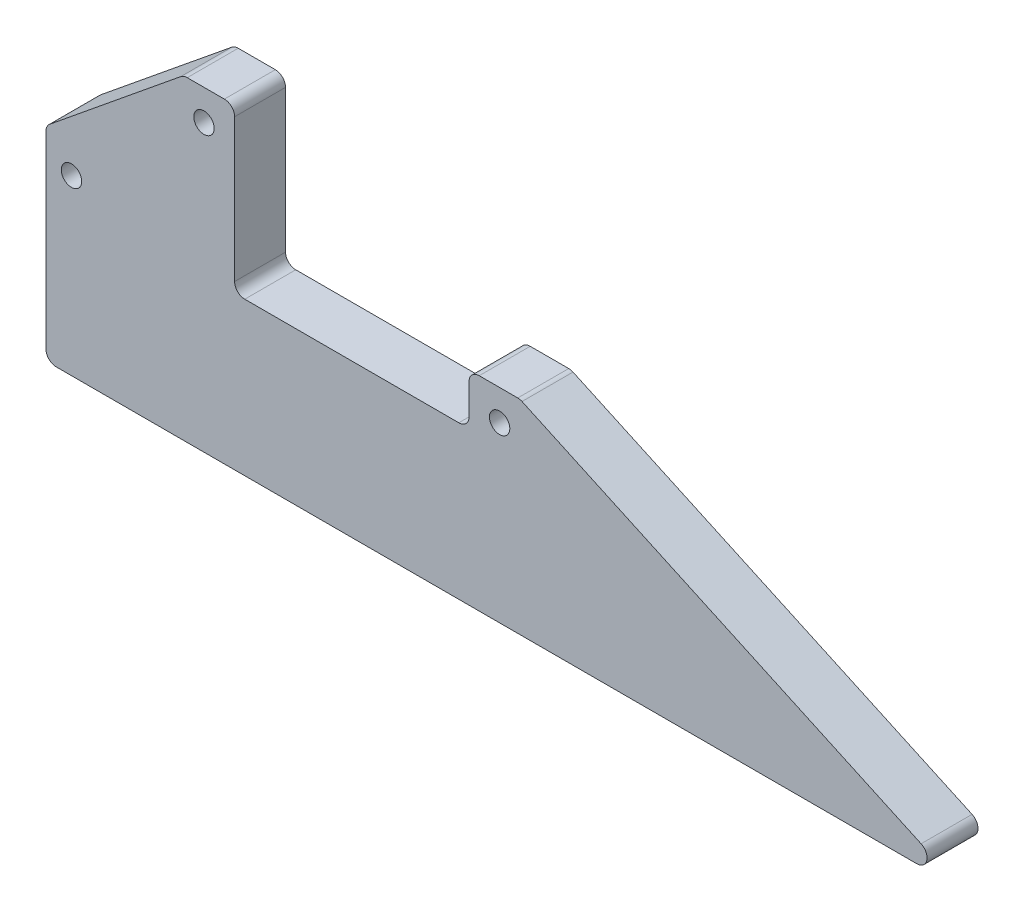
SolidWorks part; units mm, degrees
ref_plane "Front Plane" through (0, 0, 0) normal (0, 0, 1) x (1, 0, 0)
ref_plane "Top Plane" through (0, 0, 0) normal (0, 1, 0) x (1, 0, 0)
ref_plane "Right Plane" through (0, 0, 0) normal (1, 0, 0) x (0, 0, -1)
sketch "Sketch1" plane through (0, 0, 0) normal (0, 0, 1) x (1, 0, 0)
  line L1 (-87, 40) -> (0, 0)
  line L2 (0, 0) -> (-180, 0)
  line L4 (-153, 62) -> (-143, 62)
  line L5 (-143, 62) -> (-143, 30)
  line L6 (-143, 30) -> (-97, 30)
  line L7 (-97, 30) -> (-97, 40)
  line L8 (-97, 40) -> (-87, 40)
  line L9 (-153, 62) -> (-180, 40)
  line L10 (-180, 40) -> (-180, 0)
  point P3 (0, 0)
  dimension "D1" = 37
  dimension "D2" = 10
  dimension "D3" = 32
  dimension "D4" = 180
  dimension "D5" = 46
  dimension "D6" = 10
  dimension "D7" = 10
  dimension "D9" = 30
extrude "Boss-Extrude1" add sketch "Sketch1" along normal blind 10
hole_wizard "Ø4.0 (4) Diameter Hole1" positions "Sketch2" profile "Sketch3" hole size "Ø4.0" standard "ISO" end condition through all
sketch "Sketch2" plane through (0, 0, 10) normal (0, 0, 1) x (1, 0, 0)
  line L1 (-143, 30) -> (-143, 62) construction
  line L2 (-143, 62) -> (-153, 62) construction
  point P0 (-149, 56)
  point P2 (-91, 34)
  point P4 (-175, 34)
  point P24 (0, 0)
  dimension "D1" = 84
  dimension "D2" = 22
  dimension "D3" = 26
  dimension "D4" = 6
  dimension "D5" = 6
sketch "Sketch3" plane through (-149, 56, 10) normal (1, 0, 0) x (0, -1, 0)
  line L0 (0, 0) -> (0, 10)
  line L1 (0, 10) -> (2, 10)
  line L2 (2, 10) -> (2, 0)
  line L5 (2, 0) -> (0, 0)
  line L11 (0, -6.35) -> (0, 107.95) construction
  dimension "Thru Hole Dia." = 4
  dimension "Thru Hole Depth" = 10
fillet "Fillet2" radius 2 9 edges at (-143, 30, 5) (-97, 30, 5) (-97, 40, 5) (-87, 40, 5) (0, 0, 5) (-180, 0, 5) (-180, 40, 5) (-153, 62, 5) (-143, 62, 5)
